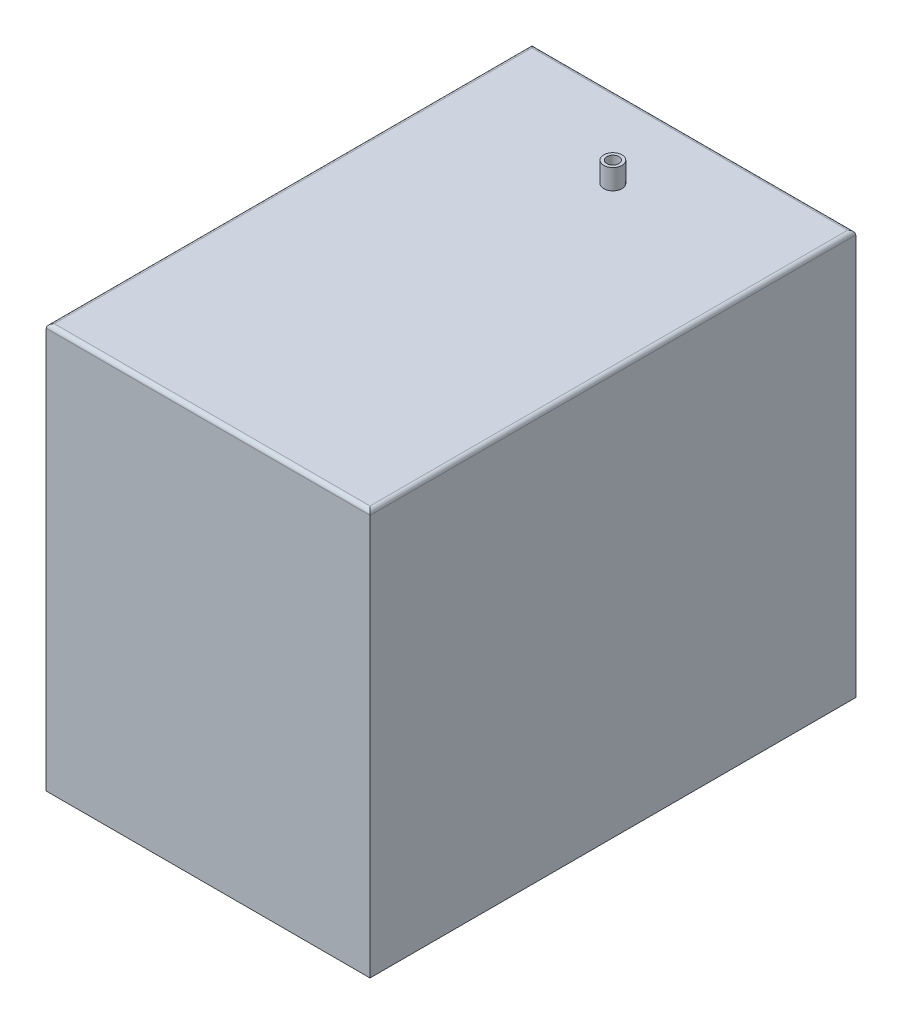
SolidWorks part; units mm, degrees
ref_plane "Front Plane" through (0, 0, 0) normal (0, 0, 1) x (1, 0, 0)
ref_plane "Top Plane" through (0, 0, 0) normal (0, 1, 0) x (1, 0, 0)
ref_plane "Right Plane" through (0, 0, 0) normal (1, 0, 0) x (0, 0, -1)
sketch "Sketch1" plane through (0, 0, 0) normal (0, 1, 0) x (1, 0, 0)
  line L1 (-40, 60) -> (40, 60)
  line L2 (-40, 60) -> (-40, -60)
  line L3 (-40, -60) -> (40, -60)
  line L4 (40, 60) -> (40, -60)
  line L5 (-40, 60) -> (40, -60) construction
  line L6 (-40, -60) -> (40, 60) construction
  point P0 (0, 0)
  dimension "D1" = 80
  dimension "D2" = 120
extrude "Boss-Extrude1" add sketch "Sketch1" along normal blind 100
sketch "Sketch2" plane through (0, 100, 0) normal (0, 1, 0) x (1, 0, 0)
  line L1 (40, 60) -> (-40, 60) construction
  circle A0 centre (0, 40) radius 1.5
  circle A1 centre (0, 40) radius 2.25
  point P5 (0, 0)
  dimension "D1" = 3
  dimension "D2" = 4.5
  dimension "D3" = 20
extrude "Boss-Extrude2" add sketch "Sketch2" along normal blind 5
fillet "Fillet1" radius 1 4 edges at (0, 100, -60) (40, 100, 0) (-40, 100, 0) (0, 100, 60)
